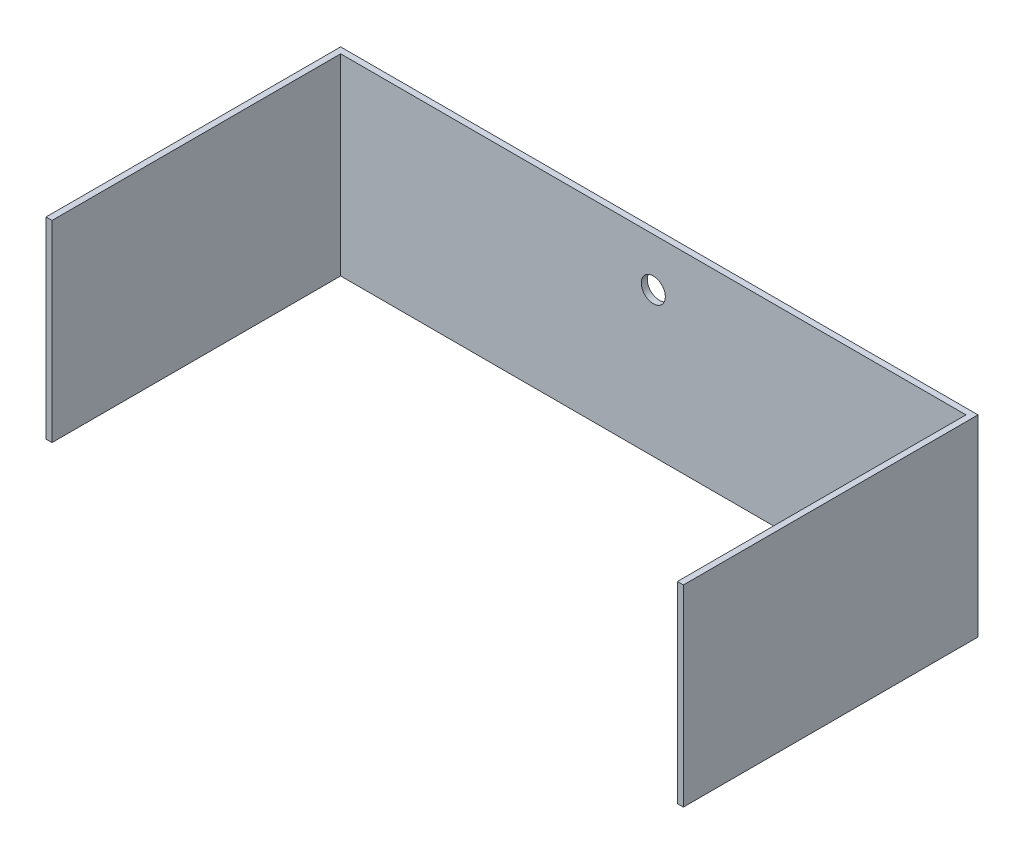
SolidWorks part; units mm, degrees
ref_plane "Front" through (0, 0, 0) normal (0, 0, 1) x (1, 0, 0)
ref_plane "Top" through (0, 0, 0) normal (0, 1, 0) x (1, 0, 0)
ref_plane "Right" through (0, 0, 0) normal (1, 0, 0) x (0, 0, -1)
sketch "Sketch1" plane through (0, 0, 0) normal (0, 1, 0) x (1, 0, 0)
  line L0 (0, 0) -> (0, 152.4)
  line L5 (0, 152.4) -> (330.2, 152.4)
  line L6 (330.2, 152.4) -> (330.2, 0)
  line L7 (330.2, 0) -> (333.375, 0)
  line L8 (333.375, 0) -> (333.375, 155.575)
  line L9 (0, 0) -> (-3.175, 0)
  line L10 (-3.175, 0) -> (-3.175, 155.575)
  line L11 (-3.175, 155.575) -> (333.375, 155.575)
  dimension "D1" = 152.4
  dimension "D2" = 330.2
  dimension "D3" = 3.175
  dimension "D4" = 3.175
  dimension "D5" = 3.175
extrude "Boss-Extrude1" add sketch "Sketch1" along normal blind 101.6
sketch "Sketch2" plane through (0, 0, -155.575) normal (0, 0, -1) x (-1, 0, 0)
  line L2 (-165.1, 101.6) -> (-165.1, 76.2) construction
  line L3 (-333.375, 101.6) -> (3.175, 101.6) construction
  circle A1 centre (-165.1, 76.2) radius 6.35
  dimension "D4" = 12.7
  dimension "D3" = 25.4
extrude "Cut-Extrude1" cut sketch "Sketch2" against normal up to next
